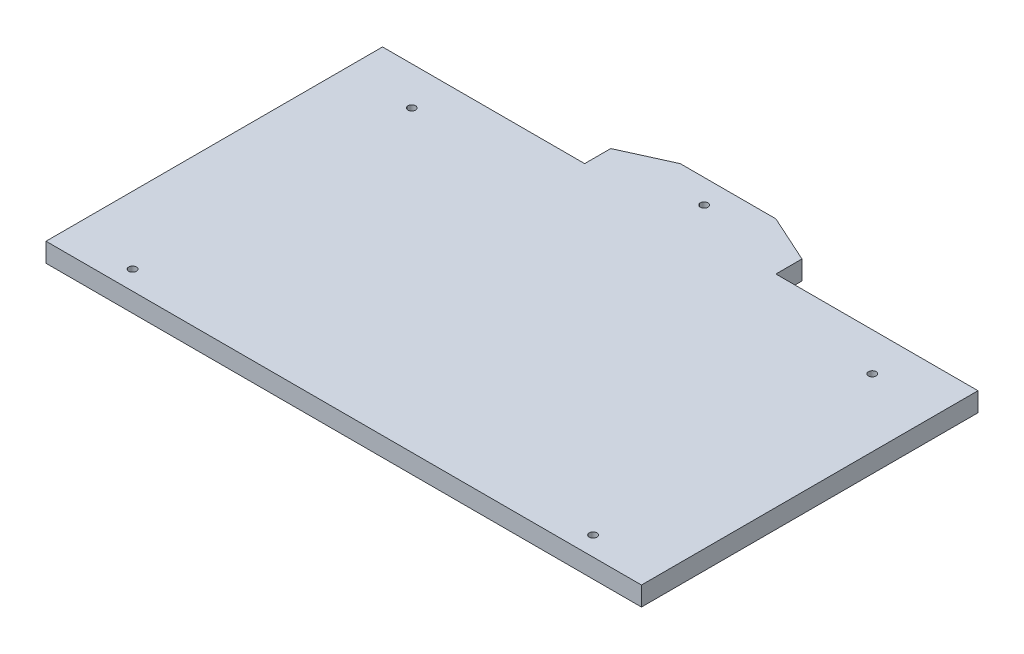
SolidWorks part; units mm, degrees
ref_plane "Front Plane" through (0, 0, 0) normal (0, 0, 1) x (1, 0, 0)
ref_plane "Top Plane" through (0, 0, 0) normal (0, 1, 0) x (1, 0, 0)
ref_plane "Right Plane" through (0, 0, 0) normal (1, 0, 0) x (0, 0, -1)
sketch "Sketch1" plane through (0, 0, 0) normal (0, 1, 0) x (1, 0, 0)
  line L0 (-60.5421, -44) -> (-57.5421, -44)
  line L1 (79.0231, -44) -> (79.0231, -34)
  line L2 (79.0231, -34) -> (-76.6797, -34)
  line L3 (-76.6797, -34) -> (-76.6797, -44)
  line L4 (-76.6797, 24) -> (79.0231, 24)
  line L5 (79.0231, 24) -> (79.0231, 44)
  line L6 (62.8855, 44) -> (59.8855, 44)
  line L7 (-76.6797, 44) -> (-76.6797, 24)
  line L8 (-76.6797, 44) -> (-76.6797, -44)
  line L9 (-60.5421, 44) -> (-57.5421, 44)
  line L10 (-60.5421, -44) -> (-57.5421, -44)
  line L11 (79.0231, 44) -> (79.0231, -44)
  line L12 (-76.6797, 34) -> (79.0231, 34) construction
  line L13 (62.8855, 44) -> (59.8855, 44)
  line L14 (59.8855, -44) -> (62.8855, -44)
  line L15 (-60.5421, -44) -> (-57.5421, -44)
  line L16 (-57.5421, 44) -> (-60.5421, 44)
  line L17 (-76.6797, -39) -> (79.0231, -39) construction
  line L18 (-57.5421, 44) -> (-60.5421, 44)
  line L19 (59.8855, 44) -> (62.8855, 44)
  line L20 (59.8855, -44) -> (62.8855, -44)
  line L21 (59.8855, -44) -> (62.8855, -44)
  line L22 (-59.0421, 44) -> (-59.0421, 24) construction
  line L23 (61.3855, 44) -> (61.3855, 24) construction
  line L24 (61.3855, -44) -> (61.3855, -34) construction
  line L25 (-59.0421, -44) -> (-59.0421, -34) construction
  line L26 (-76.6797, 24) -> (79.0231, 24)
  line L27 (79.0231, 24) -> (79.0231, 44)
  line L28 (79.0231, 44) -> (-76.6797, 44)
  line L29 (-76.6797, 44) -> (-76.6797, 24)
  line L30 (-76.6797, -44) -> (79.0231, -44)
  circle A0 centre (-59.0421, -39) radius 1.5
  circle A1 centre (61.3855, -39) radius 1.5
  circle A2 centre (61.3855, 34) radius 1.5
  circle A3 centre (-59.0421, 34) radius 1.5
  dimension "D1" = 3
extrude "Boss-Extrude2" add sketch "Sketch1" along normal blind 5 contours L11 L4 L8 L2 | L5 L28 L6 L9 L7 L4 A3 A2 | L3 L30 L0 L14 L1 L2 A1 A0
sketch "Sketch2" plane through (0, 5, 0) normal (0, 1, 0) x (1, 0, 0)
  line L0 (79.0231, 44) -> (-76.6797, 44) construction
  line L1 (-23.8283, 44) -> (26.1717, 44)
  line L2 (26.1717, 44) -> (26.1717, 50.8236)
  line L3 (26.1717, 50.8236) -> (13.6717, 56.4949)
  line L4 (13.6717, 56.4949) -> (-11.3283, 56.4949)
  line L5 (-11.3283, 56.4949) -> (-23.8283, 50.8236)
  line L6 (-23.8283, 50.8236) -> (-23.8283, 44)
  line L7 (1.1717, 56.4949) -> (1.1717, 44) construction
  circle A0 centre (1.1717, 50.2475) radius 1
  point P0 (1.1717, 44)
  dimension "D1" = 2
extrude "Boss-Extrude3" add sketch "Sketch2" against normal up to surface (5 mm away) up to face at (1.1717, 0, 0)
sketch "Sketch3" plane through (0, 5, 0) normal (0, 1, 0) x (1, 0, 0)
  circle A0 centre (61.3855, 34) radius 1.5 construction
  circle A1 centre (61.3855, -39) radius 1.5 construction
  circle A2 centre (-59.0421, -39) radius 1.5 construction
  circle A3 centre (-59.0421, 34) radius 1.5 construction
  circle A4 centre (61.3855, 34) radius 1.5
  circle A5 centre (61.3855, -39) radius 1.5
  circle A6 centre (-59.0421, -39) radius 1.5
  circle A7 centre (-59.0421, 34) radius 1.5
  circle A8 centre (61.3855, 34) radius 1
  circle A9 centre (61.3855, -39) radius 1
  circle A10 centre (-59.0421, -39) radius 1
  circle A11 centre (-59.0421, 34) radius 1
  dimension "D1" = 0.5
extrude "Boss-Extrude4" add sketch "Sketch3" against normal up to surface (5 mm away) up to face at (1.1717, 0, -30.2637)
